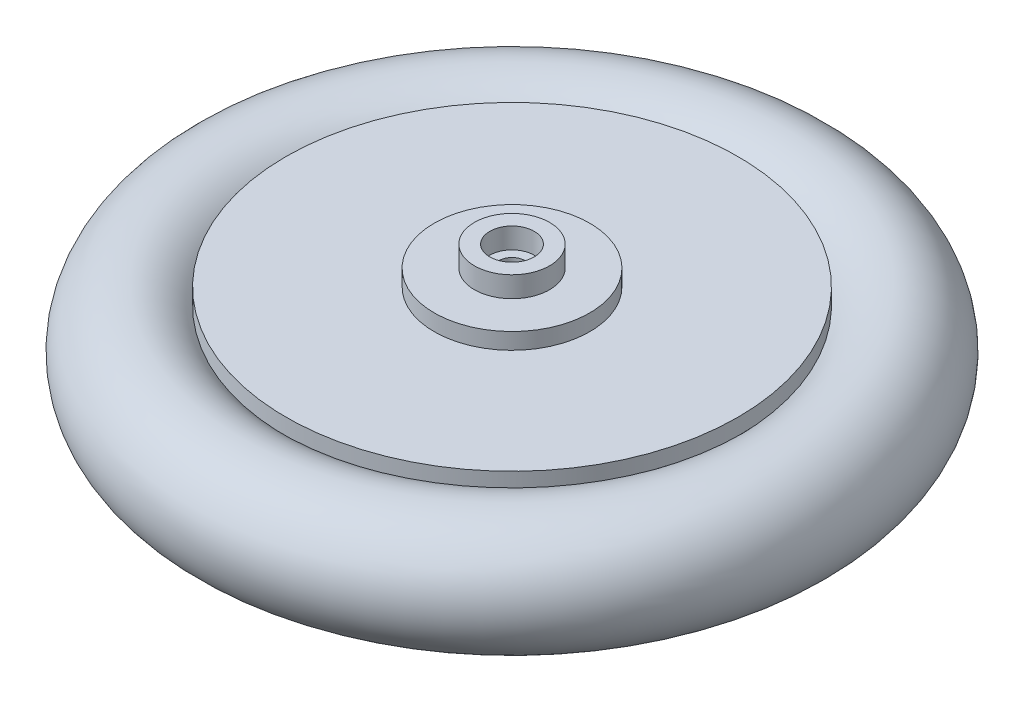
SolidWorks part; units mm, degrees
ref_plane "Plano frontal" through (0, 0, 0) normal (0, 0, 1) x (1, 0, 0)
ref_plane "Plano superior" through (0, 0, 0) normal (0, 1, 0) x (1, 0, 0)
ref_plane "Plano direito" through (0, 0, 0) normal (1, 0, 0) x (0, 0, -1)
sketch "Esboço1" plane through (0, 0, 0) normal (0, 0, 1) x (1, 0, 0)
  line L0 (1.25, 9.7) -> (2.5, 9.7)
  line L1 (0, 0) -> (44, 0) construction
  line L2 (30, 7.5) -> (10, 7.5)
  line L3 (-0.5, -17.3166) -> (-0.5, 15.353) construction
  line L4 (30, 7.5) -> (30, 5.2915)
  line L5 (30, -7.5) -> (30, -5.2915)
  line L6 (30, -7.5) -> (2.9333, -7.5)
  line L7 (2.5, 9.7) -> (2.5, 12.5)
  line L8 (2.5, 12.5) -> (4.5784, 12.5)
  line L9 (4.5784, 12.5) -> (4.5784, 9.7)
  line L10 (4.5784, 9.7) -> (10, 9.7)
  line L11 (10, 9.7) -> (10, 7.5)
  line L12 (-0.5, 9.7) -> (-0.5, -7.5)
  line L13 (2.9333, -7.5) -> (2.9333, 7.5)
  line L14 (2.9333, 7.5) -> (1.25, 7.5)
  line L15 (1.25, 7.5) -> (1.25, 9.7)
  arc A0 (30, -5.2915) -> (30, 5.2915) centre (36, 0) ccw
  dimension "D2" = 5
  dimension "D4" = 8
  dimension "D1" = 6
  dimension "D3" = 7.5
  dimension "D5" = 21
  dimension "D6" = 2.2
revolve "Revolução1" add sketch "Esboço1" angle 360 about L12
